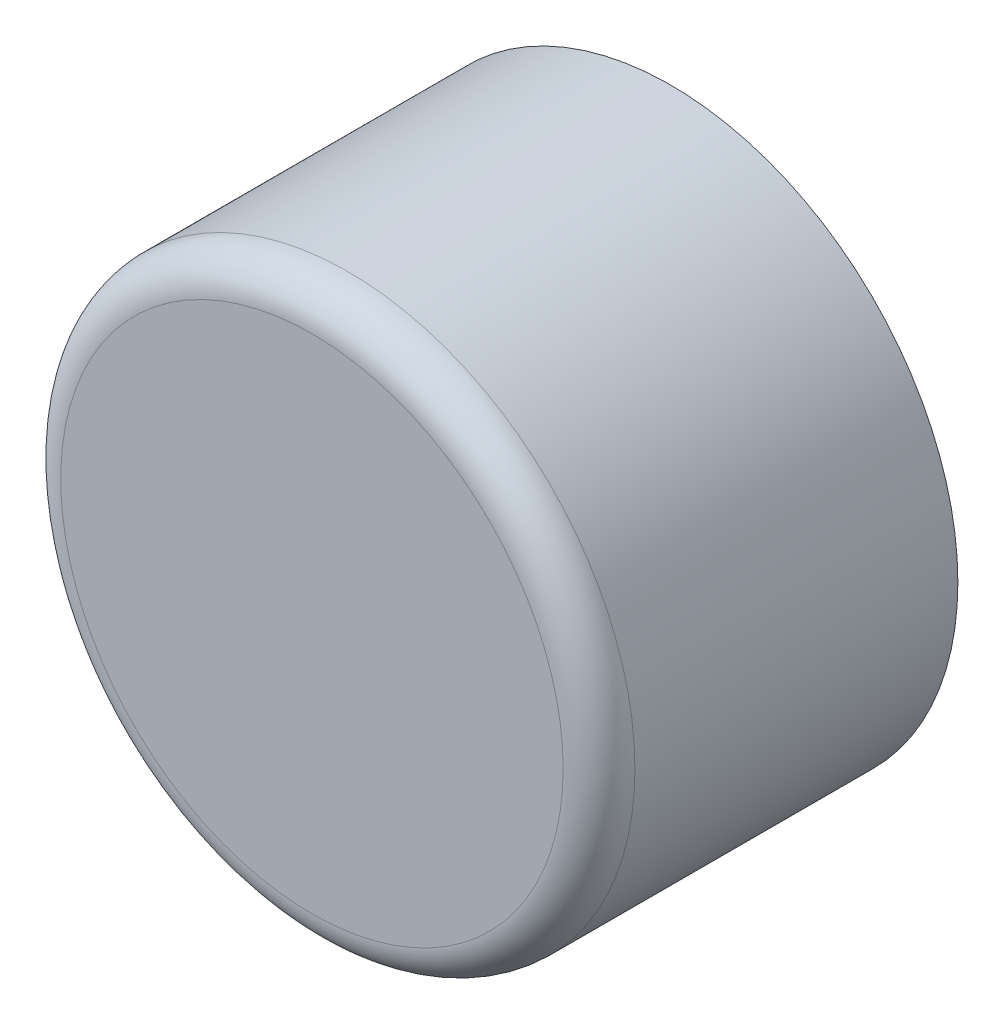
SolidWorks part; units mm, degrees
ref_plane "Front Plane" through (0, 0, 0) normal (0, 0, 1) x (1, 0, 0)
ref_plane "Top Plane" through (0, 0, 0) normal (0, 1, 0) x (1, 0, 0)
ref_plane "Right Plane" through (0, 0, 0) normal (1, 0, 0) x (0, 0, -1)
sketch "Sketch1" plane through (0, 0, 0) normal (0, 0, 1) x (1, 0, 0)
  circle A0 centre (0, 0) radius 80
  dimension "D1" = 160
extrude "Boss-Extrude1" add sketch "Sketch1" along normal blind 100
fillet "Fillet1" radius 10 1 edges at (80, 0, 100)
